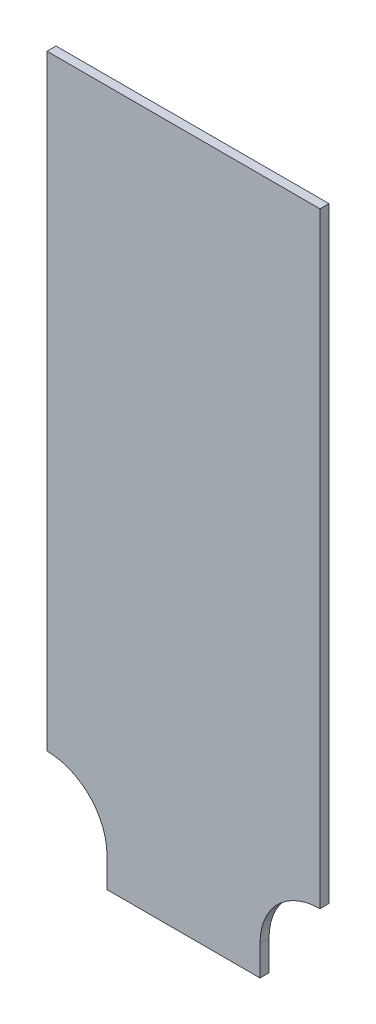
SolidWorks part; units mm, degrees
ref_plane "Face" through (0, 0, 0) normal (0, 0, 1) x (1, 0, 0)
ref_plane "Dessus" through (0, 0, 0) normal (0, 1, 0) x (1, 0, 0)
ref_plane "Droite" through (0, 0, 0) normal (1, 0, 0) x (0, 0, -1)
sketch "Esquisse1" plane through (0, 0, 0) normal (0, 0, 1) x (1, 0, 0)
  line L0 (0, 0) -> (0, 232) construction
  line L1 (45.5, 232) -> (-45.5, 232)
  line L2 (-45.5, 232) -> (-45.5, 30)
  line L3 (25.5, 0) -> (-25.5, 0)
  line L4 (-25.5, 0) -> (-25.5, 10)
  line L5 (-45.5, 30) -> (-45.5, 0) construction
  line L6 (45.5, 30) -> (45.5, 0) construction
  line L7 (25.5, 0) -> (25.5, 10)
  line L8 (45.5, 232) -> (45.5, 30)
  arc A0 (-45.5, 30) -> (-25.5, 10) centre (-45.5, 10) cw
  arc A1 (45.5, 30) -> (25.5, 10) centre (45.5, 10) ccw
  dimension "D3" = 20
  dimension "D1" = 232
  dimension "D2" = 45.5
  dimension "D4" = 30
extrude "Extrusion1" add sketch "Esquisse1" along normal blind 3
